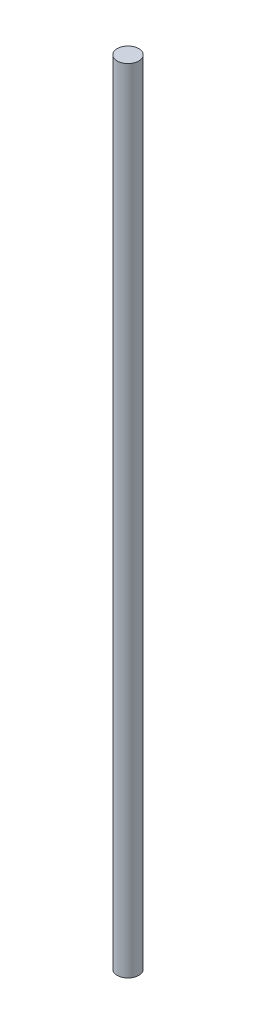
SolidWorks part; units mm, degrees
ref_plane "Front Plane" through (0, 0, 0) normal (0, 0, 1) x (1, 0, 0)
ref_plane "Top Plane" through (0, 0, 0) normal (0, 1, 0) x (1, 0, 0)
ref_plane "Right Plane" through (0, 0, 0) normal (1, 0, 0) x (0, 0, -1)
sketch "Sketch2" plane through (0, 0, 0) normal (0, 0, 1) x (1, 0, 0)
  line L0 (0, 0) -> (0, 304.1978) construction
  line L1 (0, 0) -> (-4.7625, 0)
  line L2 (0, 0) -> (0, 350)
  line L3 (-4.7625, 0) -> (-4.7625, 350)
  line L4 (0, 350) -> (-4.7625, 350)
  dimension "D1" = 350
  dimension "D2" = 4.7625
revolve "Revolve1" add sketch "Sketch2" angle 360 about L0
